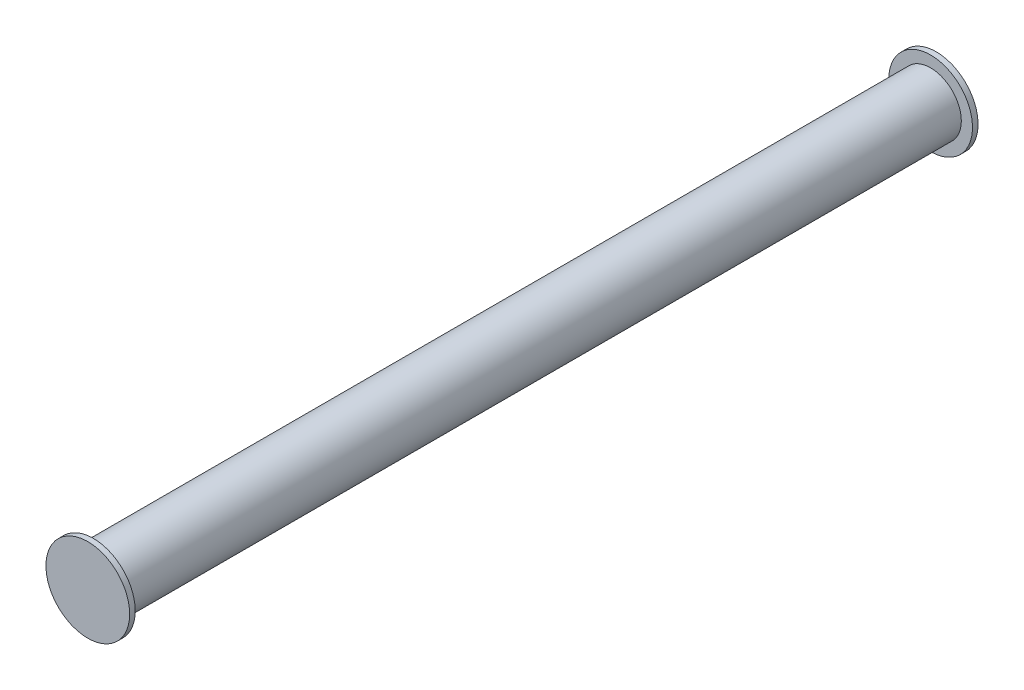
SolidWorks part; units mm, degrees
ref_plane "Front Plane" through (0, 0, 0) normal (0, 0, 1) x (1, 0, 0)
ref_plane "Top Plane" through (0, 0, 0) normal (0, 1, 0) x (1, 0, 0)
ref_plane "Right Plane" through (0, 0, 0) normal (1, 0, 0) x (0, 0, -1)
sketch "Sketch1" plane through (0, 0, 0) normal (0, 0, 1) x (1, 0, 0)
  circle A0 centre (0, 0) radius 5.5
  dimension "D1" = 11
extrude "Boss-Extrude1" add sketch "Sketch1" along normal blind 150
sketch "Sketch2" plane through (0, 0, 0) normal (0, 0, -1) x (-1, 0, 0)
  circle A0 centre (0, 0) radius 7.5
  dimension "D1" = 15
extrude "Boss-Extrude2" add sketch "Sketch2" along normal blind 1
sketch "Sketch3" plane through (0, 0, 150) normal (0, 0, 1) x (1, 0, 0)
  circle A0 centre (0, 0) radius 7.5
extrude "Boss-Extrude3" add sketch "Sketch3" along normal blind 1
